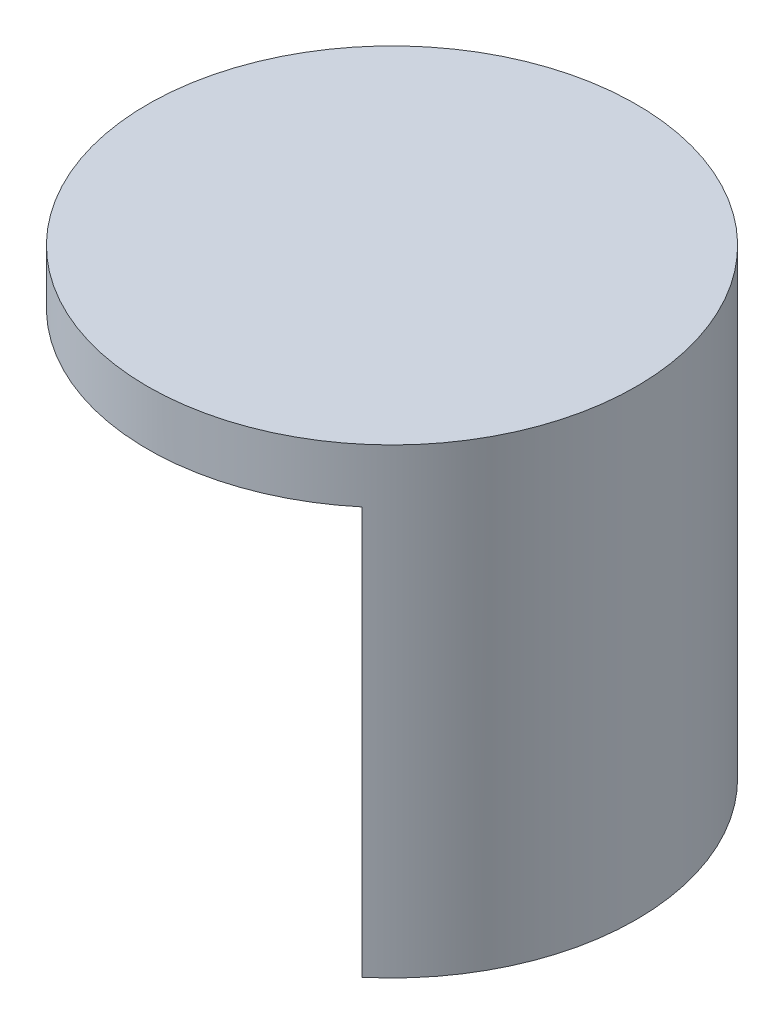
SolidWorks part; units mm, degrees
ref_plane "Ebene vorne" through (0, 0, 0) normal (0, 0, 1) x (1, 0, 0)
ref_plane "Ebene oben" through (0, 0, 0) normal (0, 1, 0) x (1, 0, 0)
ref_plane "Ebene rechts" through (0, 0, 0) normal (1, 0, 0) x (0, 0, -1)
sketch "Skizze1" plane through (0, 0, 0) normal (0, 1, 0) x (1, 0, 0)
  circle A0 centre (0, 0) radius 18
  dimension "D1" = 36
extrude "Aufsatz-Linear austragen1" add sketch "Skizze1" along normal blind 4
sketch "Skizze2" plane through (0, 0, 0) normal (0, -1, 0) x (1, 0, 0)
  line L0 (0, 0) -> (18, 0) construction
  line L1 (0, 0) -> (11.5702, 13.7888)
  line L2 (0, 0) -> (11.5702, -13.7888)
  line L3 (11.5702, 13.7888) -> (11.5702, -13.7888) construction
  circle A0 centre (0, 0) radius 10 construction
  circle A1 centre (0, 0) radius 18
  circle A2 centre (0, 0) radius 13
  point P6 (11.5702, 0)
  circle M5 centre (0, 0) radius 18
  dimension "D1" = 20
  dimension "D4" = 36
  dimension "D3" = 100
  dimension "D2" = 5
extrude "Aufsatz-Linear austragen2" add sketch "Skizze2" along normal blind 30 contours A2 L2 L1 M5
